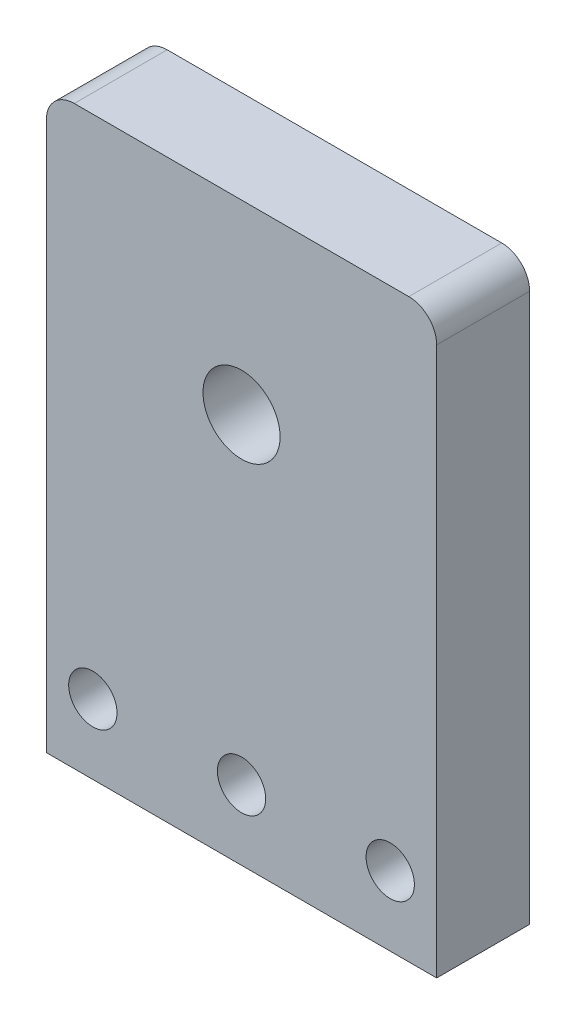
SolidWorks part; units mm, degrees
ref_plane "Front Plane" through (0, 0, 0) normal (0, 0, 1) x (1, 0, 0)
ref_plane "Top Plane" through (0, 0, 0) normal (0, 1, 0) x (1, 0, 0)
ref_plane "Right Plane" through (0, 0, 0) normal (1, 0, 0) x (0, 0, -1)
sketch "Sketch1" plane through (0, 0, 0) normal (0, 0, 1) x (1, 0, 0)
  line L1 (0, 0) -> (42, 0)
  line L2 (0, 0) -> (0, 62)
  line L3 (0, 62) -> (42, 62)
  line L4 (42, 0) -> (42, 62)
  circle A0 centre (21, 42) radius 4.15
  dimension "D3" = 8.3
  dimension "D1" = 42
  dimension "D2" = 62
  dimension "D4" = 20
extrude "Boss-Extrude1" add sketch "Sketch1" along normal blind 10
fillet "Fillet1" radius 3 2 edges at (42, 62, 5) (0, 62, 5)
sketch "Sketch2" plane through (0, 0, 10) normal (0, 0, 1) x (1, 0, 0)
  line L0 (0, 59) -> (0, 0) construction
  line L1 (42, 0) -> (42, 59) construction
  line L2 (0, 0) -> (42, 0) construction
  circle A0 centre (5, 7.5) radius 2.6
  circle A1 centre (21, 7.5) radius 2.6
  circle A2 centre (37, 7.5) radius 2.6
  dimension "D1" = 5.2
  dimension "D2" = 5.2
  dimension "D3" = 5.2
  dimension "D5" = 5
  dimension "D6" = 16
  dimension "D8" = 7.5
  dimension "D9" = 7.5
  dimension "D4" = 5
  dimension "D7" = 7.5
extrude "Cut-Extrude1" cut sketch "Sketch2" against normal through all
